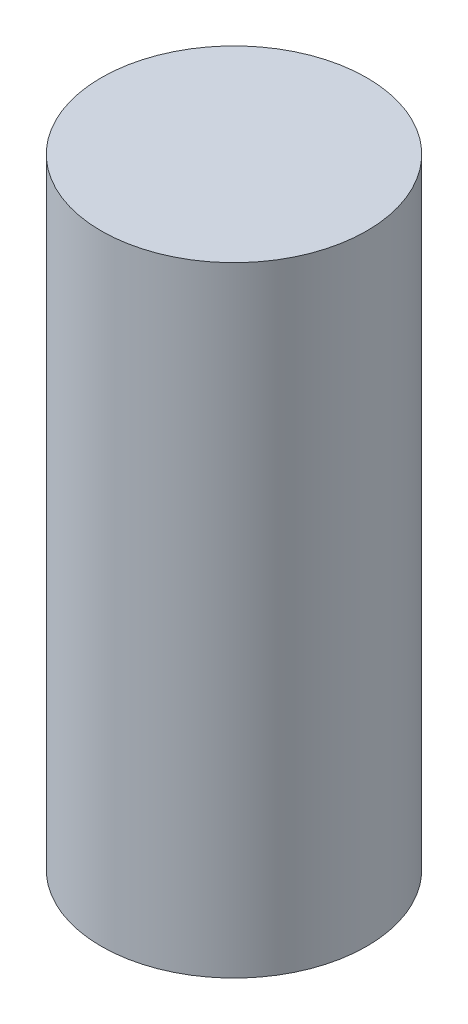
SolidWorks part; units mm, degrees
ref_plane "Front Plane" through (0, 0, 0) normal (0, 0, 1) x (1, 0, 0)
ref_plane "Top Plane" through (0, 0, 0) normal (0, 1, 0) x (1, 0, 0)
ref_plane "Right Plane" through (0, 0, 0) normal (1, 0, 0) x (0, 0, -1)
sketch "Sketch1" plane through (0, 0, 0) normal (0, 1, 0) x (1, 0, 0)
  circle A0 centre (0, 0) radius 1.5
  dimension "D1" = 3
extrude "Boss-Extrude1" add sketch "Sketch1" along normal blind 7
